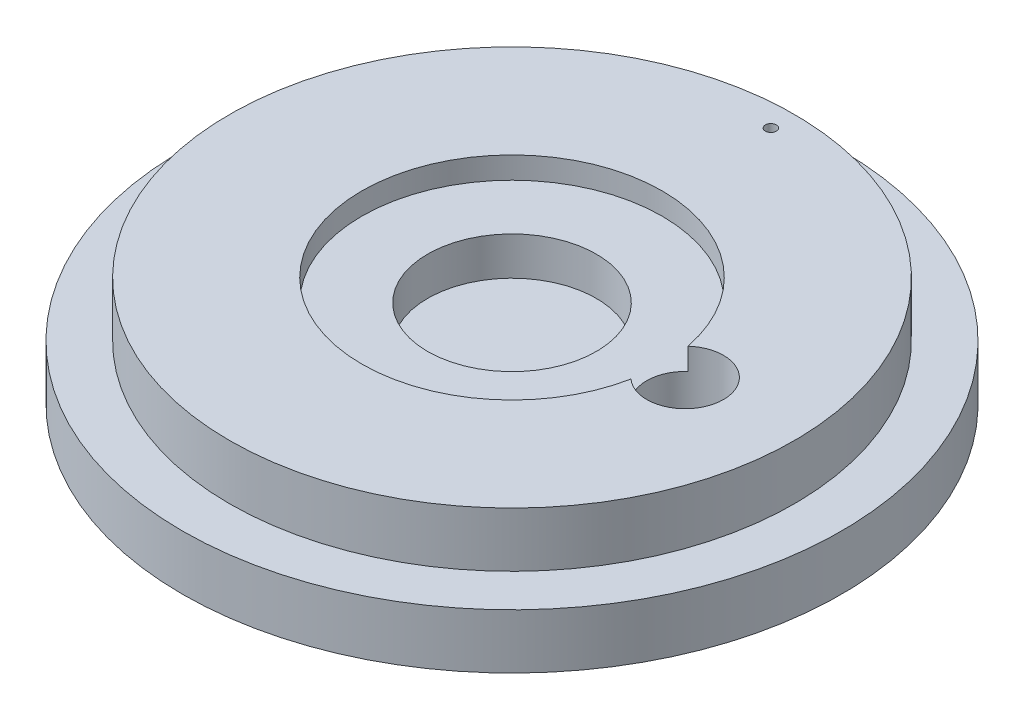
SolidWorks part; units mm, degrees
ref_plane "Front Plane" through (0, 0, 0) normal (0, 0, 1) x (1, 0, 0)
ref_plane "Top Plane" through (0, 0, 0) normal (0, 1, 0) x (1, 0, 0)
ref_plane "Right Plane" through (0, 0, 0) normal (1, 0, 0) x (0, 0, -1)
sketch "Sketch1" plane through (0, 0, 0) normal (0, 0, 1) x (1, 0, 0)
  line L0 (0, 0) -> (-30.075, 0)
  line L1 (-30.075, 0) -> (-30.075, 5)
  line L2 (-30.075, 5) -> (-25.775, 5)
  line L3 (-25.775, 5) -> (-25.775, 10)
  line L4 (-25.775, 10) -> (-13.7, 10)
  line L5 (-13.7, 10) -> (-13.7, 8)
  line L6 (-13.7, 8) -> (-7.7, 8)
  line L7 (-7.7, 8) -> (-7.7, 4.5)
  line L8 (-7.7, 4.5) -> (0, 4.5)
  line L9 (0, 4.5) -> (0, 0)
  dimension "D1" = 5
  dimension "D2" = 5
  dimension "D3" = 30.075
  dimension "D4" = 7.7
  dimension "D5" = 6
  dimension "D6" = 4.3
  dimension "D7" = 2
  dimension "D8" = 3.5
revolve "Revolve1" add sketch "Sketch1" angle 360 about L9
sketch "Sketch2" plane through (0, 10, 0) normal (0, 1, 0) x (1, 0, 0)
  circle A0 centre (15.8, 0) radius 3.5
extrude "Cut-Extrude1" cut sketch "Sketch2" against normal blind 10
sketch "Sketch3" plane through (0, 5, 0) normal (0, 1, 0) x (1, 0, 0)
  circle A0 centre (0, 23.625) radius 0.5
extrude "Cut-Extrude2" cut sketch "Sketch3" along normal mid plane 10
